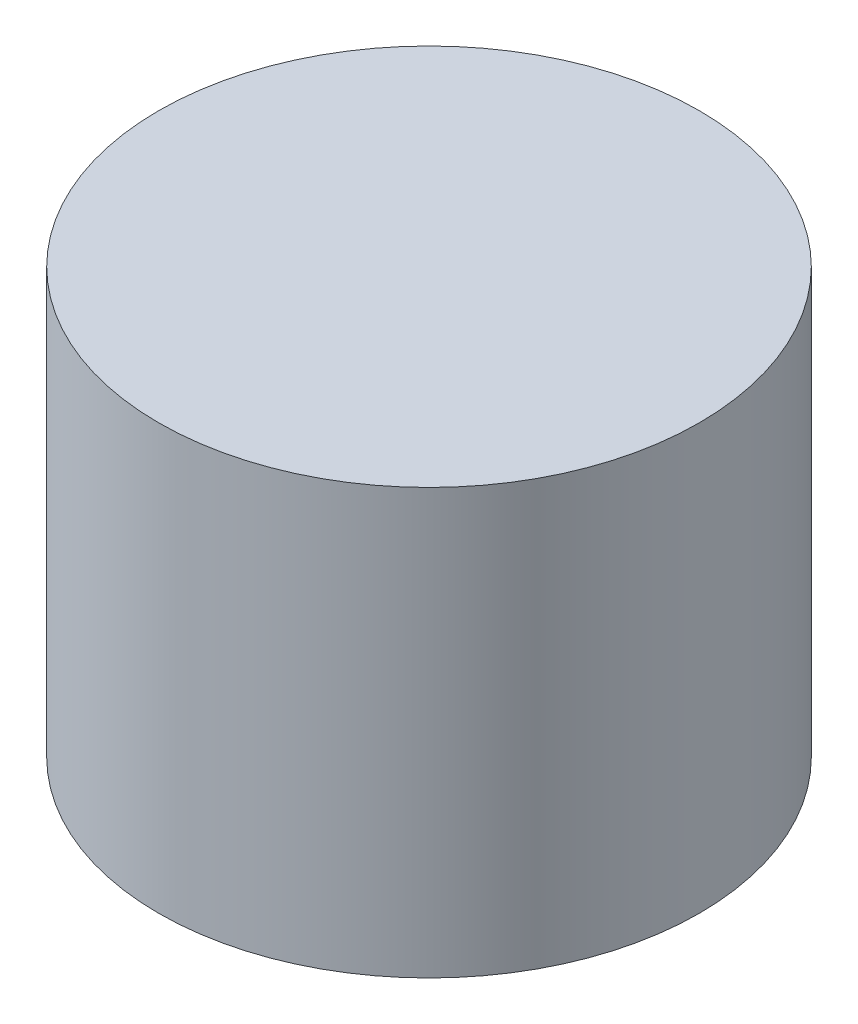
SolidWorks part; units mm, degrees
ref_plane "Front Plane" through (0, 0, 0) normal (0, 0, 1) x (1, 0, 0)
ref_plane "Top Plane" through (0, 0, 0) normal (0, 1, 0) x (1, 0, 0)
ref_plane "Right Plane" through (0, 0, 0) normal (1, 0, 0) x (0, 0, -1)
sketch "Sketch2" plane through (0, 0, 0) normal (0, 1, 0) x (1, 0, 0)
  circle A1 centre (0, 0) radius 35
extrude "Boss-Extrude1" add sketch "Sketch2" along normal blind 55
